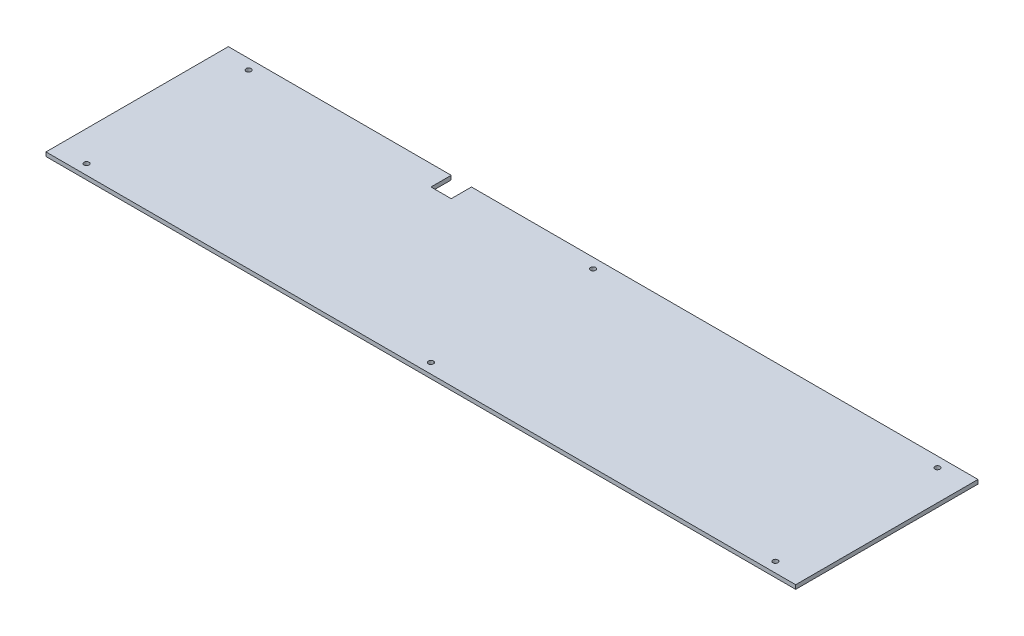
SolidWorks part; units mm, degrees
ref_plane "Front Plane" through (0, 0, 0) normal (0, 0, 1) x (1, 0, 0)
ref_plane "Top Plane" through (0, 0, 0) normal (0, 1, 0) x (1, 0, 0)
ref_plane "Right Plane" through (0, 0, 0) normal (1, 0, 0) x (0, 0, -1)
sketch "Sketch1" plane through (0, 0, 0) normal (0, 1, 0) x (1, 0, 0)
  line L0 (0, 90) -> (0, -90) construction
  line L1 (-370, -90) -> (370, -90)
  line L2 (-370, -90) -> (-370, 90)
  line L3 (-370, 90) -> (370, 90) construction
  line L4 (370, -90) -> (370, 90)
  line L5 (-370, -90) -> (370, 90) construction
  line L6 (-370, 90) -> (370, -90) construction
  line L7 (-370, 0) -> (370, 0) construction
  line L8 (-370, 90) -> (-150, 90)
  line L9 (-130, 90) -> (-150, 90) construction
  line L10 (-130, 90) -> (-130, 70)
  line L11 (-130, 70) -> (-150, 70)
  line L12 (-150, 90) -> (-150, 70)
  line L13 (-130, 90) -> (370, 90)
  circle A0 centre (-340, 80) radius 2.5
  circle A1 centre (0, 80) radius 2.5
  circle A2 centre (340, 80) radius 2.5
  circle A3 centre (-340, -80) radius 2.5
  circle A4 centre (0, -80) radius 2.5
  circle A5 centre (340, -80) radius 2.5
  point P0 (0, 0)
  dimension "D3" = 5
  dimension "D4" = 5
  dimension "D7" = 30
  dimension "D1" = 180
  dimension "D2" = 740
  dimension "D5" = 10
  dimension "D6" = 10
  dimension "D8" = 20
  dimension "D9" = 20
  dimension "D10" = 220
extrude "Boss-Extrude1" add sketch "Sketch1" along normal blind 4
